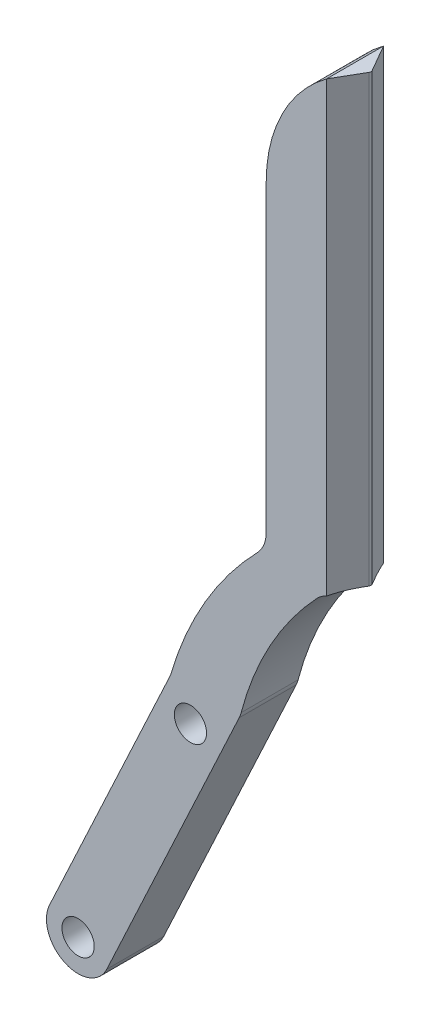
SolidWorks part; units mm, degrees
ref_plane "Front Plane" through (0, 0, 0) normal (0, 0, 1) x (1, 0, 0)
ref_plane "Top Plane" through (0, 0, 0) normal (0, 1, 0) x (1, 0, 0)
ref_plane "Right Plane" through (0, 0, 0) normal (1, 0, 0) x (0, 0, -1)
sketch "Sketch1" plane through (0, 0, 0) normal (0, 0, 1) x (1, 0, 0)
  line L0 (0, 0) -> (0, 124.6342) construction
  line L1 (0, 124.6342) -> (-11.0338, 124.6342) construction
  line L2 (-11.0338, 124.6342) -> (-11.0338, 0) construction
  line L3 (-11.0338, 0) -> (-30.1766, -41.0518)
  line L5 (-21.1135, -45.278) -> (0, 0)
  line L6 (-25.645, -43.1649) -> (-7.8951, -5.1) construction
  line L7 (-11.0338, 0) -> (0, 0) construction
  line L8 (15.1049, 25) -> (15.1049, 94.9)
  line L9 (15.1049, 25) -> (4.0712, 25) construction
  line L10 (4.0712, 25) -> (4.0712, 75)
  arc A0 (-30.1766, -41.0518) -> (-21.1135, -45.278) centre (-25.645, -43.1649) ccw
  circle A1 centre (-25.645, -43.1649) radius 2.55
  circle A2 centre (-7.8951, -5.1) radius 2.55
  arc A3 (0, 0) -> (15.1049, 25) centre (48.4814, -12.2292) cw
  arc A4 (-11.0338, 0) -> (4.0712, 25) centre (43.1149, -15.6533) cw
  arc A5 (4.0712, 75) -> (15.1049, 94.9) centre (27.5334, 75) cw
  dimension "D2" = 5
  dimension "D3" = 5.1
  dimension "D10" = 50
  dimension "D1" = 155
  dimension "D4" = 42
  dimension "D5" = 5.1
  dimension "D6" = 23
  dimension "D7" = 100
  dimension "D8" = 50
  dimension "D9" = 25
extrude "Boss-Extrude1" add sketch "Sketch1" along normal blind 9
sketch "Sketch2" plane through (0, 0, 9) normal (0, 0, 1) x (1, 0, 0)
  line L1 (15.1049, 94.9) -> (13.6049, 94.9)
  line L2 (15.1049, 94.9) -> (15.1049, 23.5986)
  line L3 (15.1049, 23.5986) -> (13.6049, 23.5986)
  line L4 (13.6049, 94.9) -> (13.6049, 23.5986)
  arc A0 (15.1049, 25) -> (0, 0) centre (48.4814, -12.2292) ccw construction
  dimension "D1" = 1.5
extrude "Cut-Extrude1" cut sketch "Sketch2" against normal through all
ref_plane "Plane1" through (0, 93.8805, 0) normal (0, -1, 0) x (0, 0, -1)
sketch "Sketch4" plane through (0, 93.8805, 0) normal (0, -1, 0) x (0, 0, -1)
  line L0 (0, 13.6049) -> (-4.5, 16.203)
  line L1 (-4.5, 16.203) -> (-9, 13.6049)
  line L2 (-9, 13.6049) -> (0, 13.6049)
  line L3 (-4.5, 13.6049) -> (-4.5, 16.203) construction
  dimension "D1" = 120
extrude "Boss-Extrude2" add sketch "Sketch4" along normal up to vertex (70.2819 mm away)
fillet "Fillet1" radius 0.5 1 edges at (16.203, 58.7396, 4.5)
fillet "Fillet2" radius 5 4 edges at (0, 0, 4.5) (13.6049, 23.5986, 4.5) (-11.0338, 0, 4.5) (4.0712, 25, 4.5)
